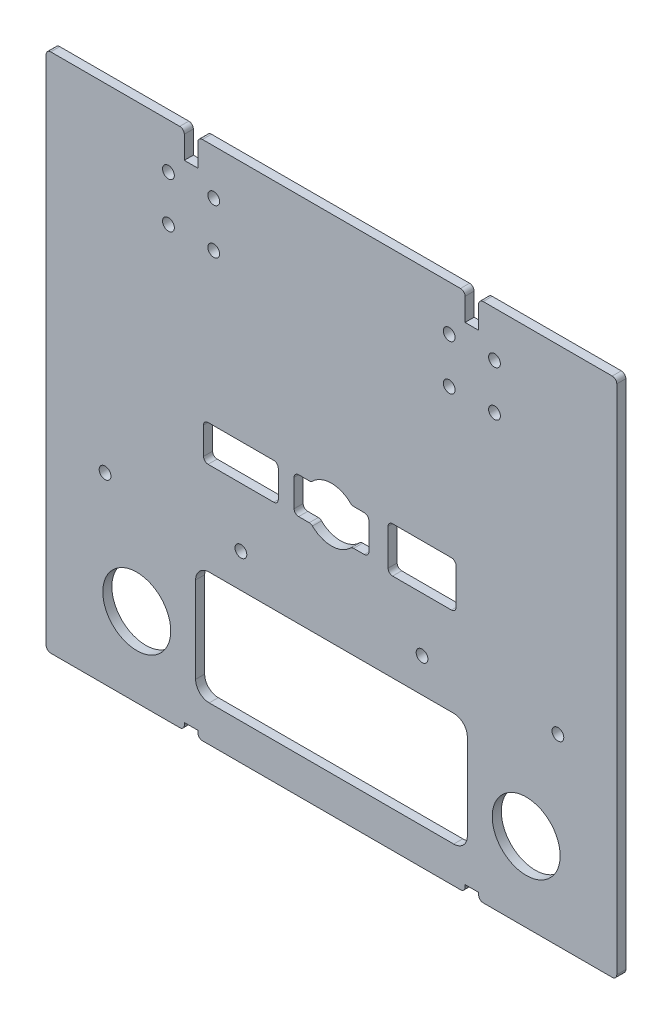
SolidWorks part; units mm, degrees
ref_plane "Front Plane" through (0, 0, 0) normal (0, 0, 1) x (1, 0, 0)
ref_plane "Top Plane" through (0, 0, 0) normal (0, 1, 0) x (1, 0, 0)
ref_plane "Right Plane" through (0, 0, 0) normal (1, 0, 0) x (0, 0, -1)
sketch "Sketch1" plane through (0, 0, 0) normal (0, 0, 1) x (1, 0, 0)
  line L1 (-63, 57.5) -> (63, 57.5)
  line L2 (-63, 57.5) -> (-63, -57.5)
  line L3 (-63, -57.5) -> (63, -57.5)
  line L4 (63, 57.5) -> (63, -57.5)
  line L5 (-63, 57.5) -> (63, -57.5) construction
  line L6 (-63, -57.5) -> (63, 57.5) construction
  point P0 (0, 0)
  dimension "D1" = 126
  dimension "D2" = 115
extrude "Boss-Extrude1" add sketch "Sketch1" along normal blind 2
sketch "Sketch2" plane through (0, 0, 2) normal (0, 0, 1) x (1, 0, 0)
  line L0 (-43, -40) -> (43, -40) construction
  line L1 (0, 0) -> (0, -40) construction
  line L3 (-30, -24.5) -> (30, -24.5)
  line L4 (-30, -24.5) -> (-30, -49.5)
  line L5 (-30, -49.5) -> (30, -49.5)
  line L6 (30, -24.5) -> (30, -49.5)
  line L7 (-30, -24.5) -> (30, -49.5) construction
  line L8 (-30, -49.5) -> (30, -24.5) construction
  line L9 (-63, -57.5) -> (63, -57.5) construction
  circle A0 centre (-43, -40) radius 7.5
  circle A1 centre (43, -40) radius 7.5
  point P7 (0, -37)
  dimension "D1" = 15
  dimension "D2" = 86
  dimension "D3" = 40
  dimension "D4" = 60
  dimension "D5" = 25
  dimension "D6" = 8
extrude "Cut-Extrude1" cut sketch "Sketch2" against normal blind 2 contours A0 | A1 | L6 L3 L4 L5
fillet "Fillet1" radius 3 4 edges at (30, -49.5, 1) (-30, -49.5, 1) (30, -24.5, 1) (-30, -24.5, 1)
sketch "Sketch3" plane through (0, 0, 2) normal (0, 0, 1) x (1, 0, 0)
  line L0 (-30, 57.5) -> (-30, 0) construction
  line L1 (63, 57.5) -> (-63, 57.5) construction
  line L2 (0, 0) -> (0, 57.5) construction
  circle A0 centre (-26, 47.5) radius 1.3
  circle A1 centre (-36, 47.5) radius 1.3
  circle A2 centre (36, 47.5) radius 1.3
  circle A3 centre (26, 47.5) radius 1.3
  circle A4 centre (-26, 37.5) radius 1.3
  circle A5 centre (-36, 37.5) radius 1.3
  circle A6 centre (36, 37.5) radius 1.3
  circle A7 centre (26, 37.5) radius 1.3
  dimension "D5" = 2.6
  dimension "D1" = 30
  dimension "D2" = 4
  dimension "D3" = 6
  dimension "D4" = 10
  dimension "D7" = 10
  dimension "D6" = 2
extrude "Cut-Extrude2" cut sketch "Sketch3" against normal blind 4
sketch "Sketch4" plane through (0, 0, 0) normal (0, 0, -1) x (-1, 0, 0)
  line L0 (-63, 57.5) -> (63, 57.5) construction
  line L1 (-36, 47.5) -> (36, 47.5) construction
  line L2 (-36, 47.5) -> (-36, 57.5) construction
  line L3 (-36, 57.5) -> (36, 57.5) construction
  line L4 (36, 47.5) -> (36, 57.5) construction
  line L5 (-26, 47.5) -> (-26, 57.5) construction
  line L6 (26, 47.5) -> (26, 57.5) construction
  line L7 (-36, 57.5) -> (-26, 47.5) construction
  line L8 (-26, 57.5) -> (-36, 47.5) construction
  line L9 (26, 57.5) -> (36, 47.5) construction
  line L10 (26, 47.5) -> (36, 57.5) construction
  line L11 (-31, 52.5) -> (-31, 57.5) construction
  line L12 (31, 52.5) -> (31, 57.5) construction
  line L13 (63, -57.5) -> (-63, -57.5) construction
  line L14 (-32.5, 57.5) -> (-29.5, 57.5)
  line L15 (-32.5, 57.5) -> (-32.5, 51.5)
  line L16 (-32.5, 51.5) -> (-29.5, 51.5)
  line L17 (-29.5, 57.5) -> (-29.5, 51.5)
  line L18 (29.5, 57.5) -> (32.5, 57.5)
  line L19 (29.5, 57.5) -> (29.5, 51.5)
  line L20 (29.5, 51.5) -> (32.5, 51.5)
  line L21 (32.5, 57.5) -> (32.5, 51.5)
  line L22 (32.5, -57.5) -> (29.5, -57.5)
  line L23 (32.5, -57.5) -> (32.5, -56)
  line L24 (32.5, -56) -> (29.5, -56)
  line L25 (29.5, -57.5) -> (29.5, -56)
  line L27 (-32.5, -57.5) -> (-29.5, -57.5)
  line L28 (-32.5, -57.5) -> (-32.5, -56)
  line L29 (-32.5, -56) -> (-29.5, -56)
  line L30 (-29.5, -57.5) -> (-29.5, -56)
  dimension "D1" = 1
  dimension "D2" = 1.5
  dimension "D3" = 1.5
  dimension "D4" = 1
  dimension "D5" = 1.5
  dimension "D6" = 1.5
  dimension "D7" = 1.5
extrude "Cut-Extrude3" cut sketch "Sketch4" against normal blind 10
fillet "Fillet2" radius 1 12 edges at (-32.5, 57.5, 1) (-29.5, 57.5, 1) (29.5, 57.5, 1) (32.5, 57.5, 1) (-63, 57.5, 1) (63, 57.5, 1) (-63, -57.5, 1) (63, -57.5, 1) (32.5, -57.5, 1) (29.5, -57.5, 1) (-29.5, -57.5, 1) (-32.5, -57.5, 1)
sketch "Sketch6" plane through (0, 0, 2) normal (0, 0, 1) x (1, 0, 0)
  line L1 (-8.25, 4) -> (8.25, 4)
  line L2 (-8.25, 4) -> (-8.25, -4)
  line L3 (-8.25, -4) -> (8.25, -4)
  line L4 (8.25, 4) -> (8.25, -4)
  line L5 (-8.25, 4) -> (8.25, -4) construction
  line L6 (-8.25, -4) -> (8.25, 4) construction
  line L7 (12.5, 5) -> (27.5, 5)
  line L8 (12.5, 5) -> (12.5, -5)
  line L9 (12.5, -5) -> (27.5, -5)
  line L10 (27.5, 5) -> (27.5, -5)
  line L11 (12.5, 5) -> (27.5, -5) construction
  line L12 (12.5, -5) -> (27.5, 5) construction
  line L17 (-28.25, 4) -> (-11.75, 4)
  line L18 (-28.25, 4) -> (-28.25, -4)
  line L19 (-28.25, -4) -> (-11.75, -4)
  line L20 (-11.75, 4) -> (-11.75, -4)
  line L21 (-28.25, 4) -> (-11.75, -4) construction
  line L22 (-28.25, -4) -> (-11.75, 4) construction
  circle A0 centre (0, 0) radius 6
  point P0 (0, 0)
  point P7 (20, 0)
  point P21 (-20, 0)
  dimension "D3" = 12
  dimension "D1" = 16.5
  dimension "D2" = 8
  dimension "D4" = 10
  dimension "D5" = 15
  dimension "D6" = 20
  dimension "D8" = 20
extrude "Cut-Extrude5" cut sketch "Sketch6" against normal blind 10 contours L10 L7 L8 L9 | L1 A0 L3 | A0 L3 L4 L1 | L1 A0 | A0 L1 L2 L3 | L3 A0 | L20 L17 L18 L19
fillet "Fillet3" radius 1 16 edges at (12.5, 5, 1) (27.5, 5, 1) (27.5, -5, 1) (12.5, -5, 1) (-8.25, -4, 1) (-4.4721, -4, 1) (4.4721, -4, 1) (8.25, -4, 1) (8.25, 4, 1) (4.4721, 4, 1) (-4.4721, 4, 1) (-8.25, 4, 1) (-11.75, 4, 1) (-11.75, -4, 1) (-28.25, -4, 1) (-28.25, 4, 1)
sketch "Sketch7" plane through (0, 0, 0) normal (0, 0, -1) x (-1, 0, 0)
  line L0 (-63, -17) -> (63, -17) construction
  line L1 (-63, -56.5) -> (-63, 56.5) construction
  line L2 (63, 56.5) -> (63, -56.5) construction
  circle A0 centre (-50, -17) radius 1.3
  circle A1 centre (-20, -17) radius 1.3
  circle A2 centre (20, -17) radius 1.3
  circle A3 centre (50, -17) radius 1.3
  dimension "D6" = 2.6
  dimension "D1" = 17
  dimension "D2" = 20
  dimension "D3" = 20
  dimension "D4" = 30
  dimension "D5" = 30
extrude "Cut-Extrude6" cut sketch "Sketch7" against normal blind 2.5
